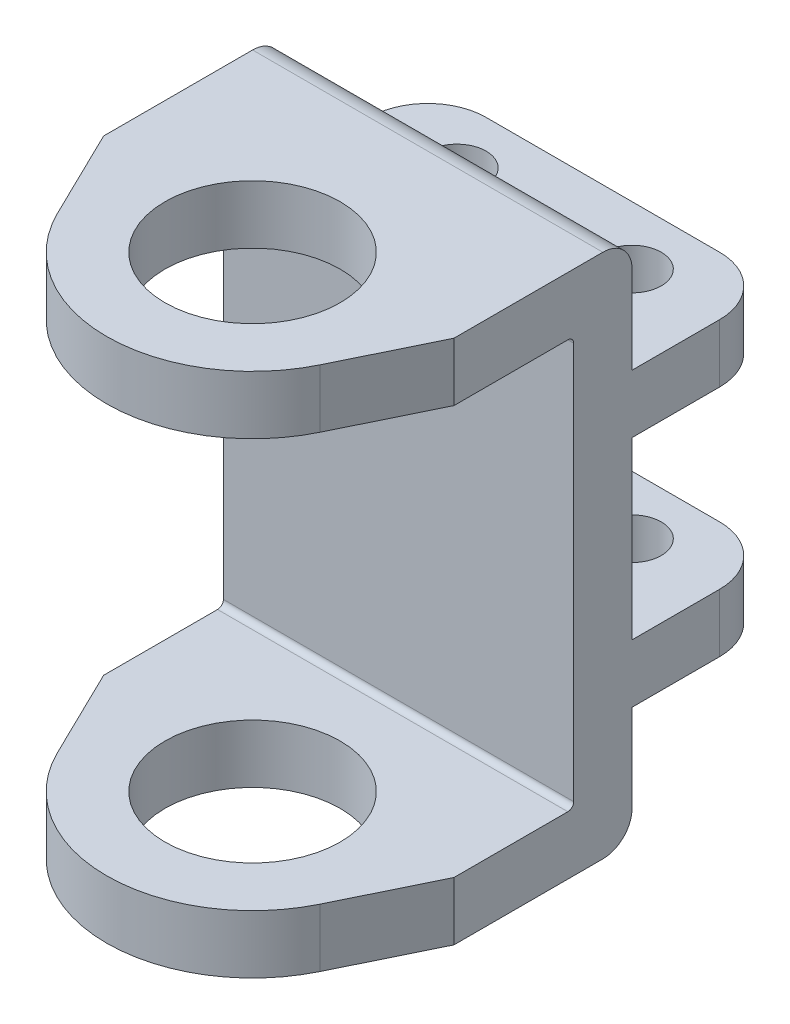
SolidWorks part; units mm, degrees
ref_plane "Front Plane" through (0, 0, 0) normal (0, 0, 1) x (1, 0, 0)
ref_plane "Top Plane" through (0, 0, 0) normal (0, 1, 0) x (1, 0, 0)
ref_plane "Right Plane" through (0, 0, 0) normal (1, 0, 0) x (0, 0, -1)
sketch "Sketch1" plane through (0, 0, 0) normal (0, 1, 0) x (1, 0, 0)
  line L0 (-205.5819, 0) -> (290.4962, 0) construction
  line L1 (290.4962, 0) -> (0, 279.8559) construction
  line L2 (0, 279.8559) -> (0, 17.5) construction
  line L3 (-30, 32.5) -> (30, 32.5) construction
  line L5 (30, 0) -> (30, 32.5)
  line L6 (20, 42.5) -> (-20, 42.5)
  line L7 (-30, 0) -> (-30, 32.5)
  line L8 (0, 0) -> (0, -30.281) construction
  line L9 (30, 42.5) -> (12.3529, 17.5) construction
  line L10 (30, 32.5) -> (30, 0) construction
  line L11 (-40, -17.5) -> (40, -17.5) construction
  line L12 (-30, 0) -> (-30, 17.5) construction
  line L13 (-30, 17.5) -> (30, 17.5) construction
  line L15 (-30, -13.0128) -> (-22.4719, -28.4551)
  line L16 (-12.3529, 17.5) -> (-30, 42.5) construction
  line L17 (-30, 0) -> (-30, -13.0128)
  line L19 (30, 0) -> (30, -13.0128)
  line L20 (30, -13.0128) -> (22.4719, -28.4551)
  circle A0 centre (-15, 32.5) radius 5
  arc A3 (30, 32.5) -> (20, 42.5) centre (20, 32.5) ccw
  arc A4 (-30, 32.5) -> (-20, 42.5) centre (-20, 32.5) cw
  circle A5 centre (15, 32.5) radius 5
  arc A6 (-22.4719, -28.4551) -> (22.4719, -28.4551) centre (0, -17.5) ccw
  circle A7 centre (0, -17.5) radius 15
  point P4 (0, 0)
  dimension "D5" = 10
  dimension "D6" = 60
  dimension "D7" = 80
  dimension "D1" = 15
  dimension "D2" = 60
  dimension "D3" = 10
  dimension "D4" = 15
extrude "Boss-Extrude1" add sketch "Sketch1" along normal blind 90
sketch "Sketch2" plane through (30, 0, 0) normal (1, 0, 0) x (0, 0, -1)
  line L0 (-42.5, 90) -> (-42.5, 0) construction
  line L1 (-42.5, 80) -> (6.5, 80)
  line L2 (-42.5, 80) -> (-42.5, 10)
  line L3 (-42.5, 10) -> (6.5, 10)
  line L4 (7.5, 79) -> (7.5, 11)
  line L5 (-13.0128, 90) -> (32.5, 90) construction
  line L6 (17.5, 90) -> (42.5, 90)
  line L7 (17.5, 90) -> (17.5, 70)
  line L8 (17.5, 70) -> (42.5, 70)
  line L9 (42.5, 90) -> (42.5, 70)
  line L10 (42.5, 90) -> (42.5, 0) construction
  line L11 (-42.5, 0) -> (-28.4551, 0) construction
  line L12 (42.5, 0) -> (17.5, 0)
  line L13 (42.5, 0) -> (42.5, 20)
  line L14 (42.5, 20) -> (17.5, 20)
  line L15 (17.5, 0) -> (17.5, 20)
  line L16 (42.5, 60) -> (17.5, 60)
  line L17 (42.5, 60) -> (42.5, 30)
  line L18 (42.5, 30) -> (17.5, 30)
  line L19 (17.5, 60) -> (17.5, 30)
  arc A0 (7.5, 11) -> (6.5, 10) centre (6.5, 11) cw
  arc A1 (7.5, 79) -> (6.5, 80) centre (6.5, 79) ccw
  point P25 (9.7436, 90)
  point P30 (7.5, 80)
  dimension "D11" = 1
  dimension "D1" = 25
  dimension "D2" = 70
  dimension "D3" = 10
  dimension "D4" = 50
  dimension "D5" = 30
  dimension "D6" = 30
  dimension "D7" = 20
  dimension "D8" = 20
  dimension "D9" = 25
  dimension "D10" = 25
extrude "Cut-Extrude1" cut sketch "Sketch2" against normal through all
fillet "Fillet1" radius 5 2 edges at (0, 0, -17.5) (0, 90, -17.5)
